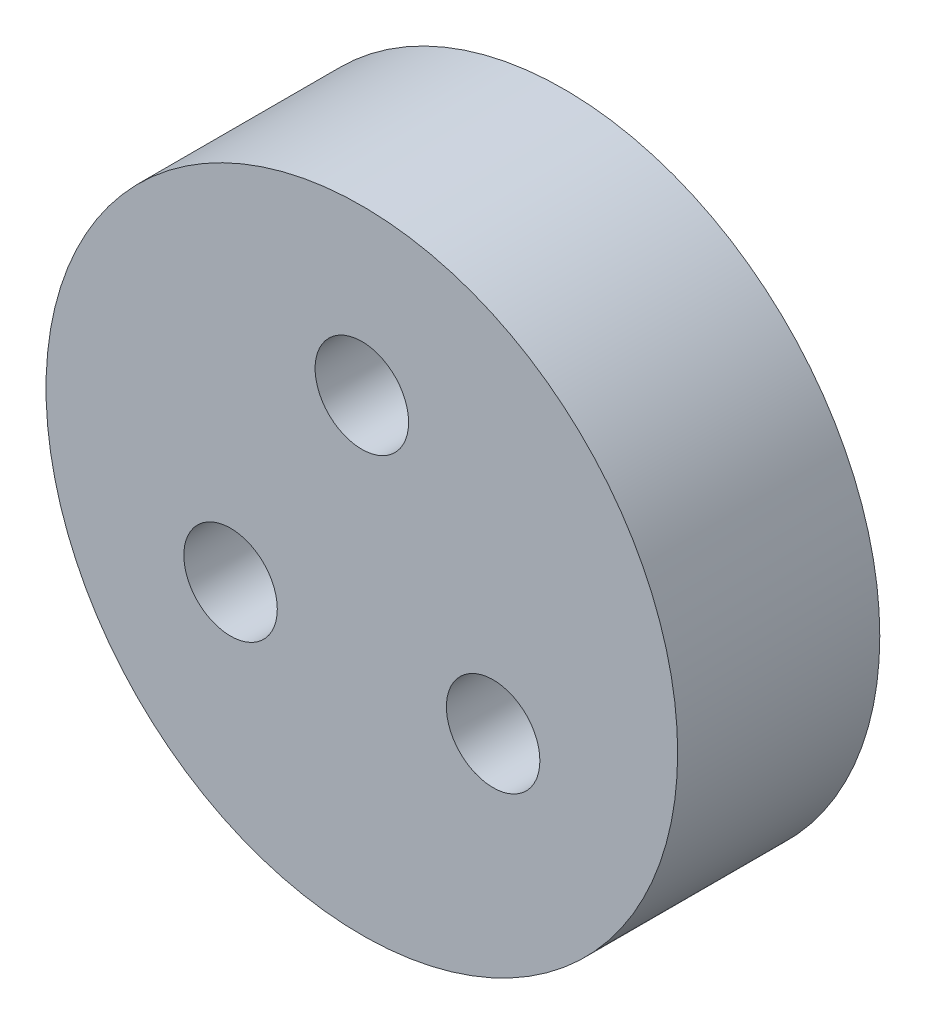
SolidWorks part; units mm, degrees
ref_plane "Front Plane" through (0, 0, 0) normal (0, 0, 1) x (1, 0, 0)
ref_plane "Top Plane" through (0, 0, 0) normal (0, 1, 0) x (1, 0, 0)
ref_plane "Right Plane" through (0, 0, 0) normal (1, 0, 0) x (0, 0, -1)
sketch "Sketch1" plane through (0, 0, 0) normal (0, 0, 1) x (1, 0, 0)
  circle A0 centre (0, 0) radius 12.5
  dimension "D1" = 25
extrude "Boss-Extrude1" add sketch "Sketch1" along normal blind 8
sketch "Sketch2" plane through (0, 0, 8) normal (0, 0, 1) x (1, 0, 0)
  circle A0 centre (0, 6) radius 1.85
  dimension "D1" = 3.7
  dimension "D2" = 6
extrude "Cut-Extrude1" cut sketch "Sketch2" against normal up to next (8 mm away)
sketch "Sketch3" plane through (0, 0, 0) normal (0, 0, -1) x (-1, 0, 0)
  line L1 (3.2332, 6) -> (1.6166, 8.8)
  line L2 (1.6166, 8.8) -> (-1.6166, 8.8)
  line L3 (-1.6166, 8.8) -> (-3.2332, 6)
  line L4 (-3.2332, 6) -> (-1.6166, 3.2)
  line L5 (-1.6166, 3.2) -> (1.6166, 3.2)
  line L6 (1.6166, 3.2) -> (3.2332, 6)
  circle A0 centre (0, 6) radius 2.8 construction
  dimension "D1" = 5.6
extrude "Cut-Extrude2" cut sketch "Sketch3" against normal blind 5
pattern_circular "CirPattern1" count 3 over 360 about axis through (0, 0, 0) along (0, 0, 1) of "Cut-Extrude1", "Cut-Extrude2"
